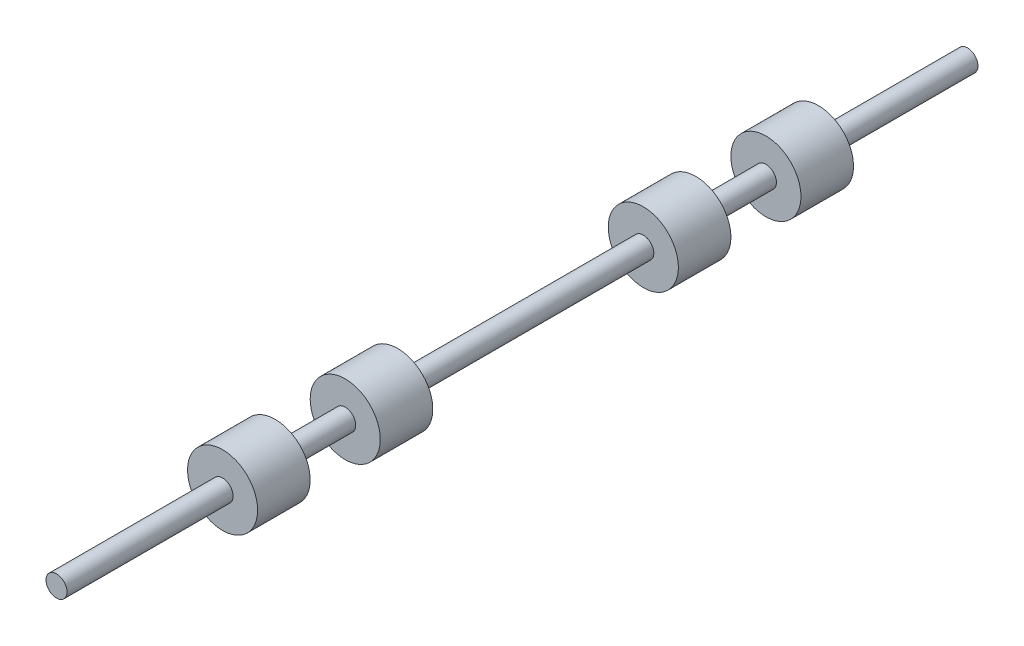
SolidWorks part; units mm, degrees
ref_plane "Front Plane" through (0, 0, 0) normal (0, 0, 1) x (1, 0, 0)
ref_plane "Top Plane" through (0, 0, 0) normal (0, 1, 0) x (1, 0, 0)
ref_plane "Right Plane" through (0, 0, 0) normal (1, 0, 0) x (0, 0, -1)
sketch "Sketch1" plane through (0, 0, 0) normal (0, 0, 1) x (1, 0, 0)
  circle A0 centre (0, 0) radius 0.3
  dimension "D1" = 0.6
extrude "Boss-Extrude1" add sketch "Sketch1" along normal blind 26
sketch "Sketch2" plane through (0, 0, 0) normal (0, 1, 0) x (1, 0, 0)
  line L0 (0, 0) -> (0, -26) construction
  line L1 (-0.3, -26) -> (0.3, -26) construction
  line L2 (0, -6.753) -> (3.292, -6.753) construction
  line L11 (0, -18.76) -> (3.292, -18.76) construction
  line L21 (0, -4.253) -> (1, -4.253)
  line L22 (0, -4.253) -> (0, -5.753)
  line L23 (0, -5.753) -> (1, -5.753)
  line L24 (1, -4.253) -> (1, -5.753)
  line L25 (0, -7.753) -> (1, -7.753)
  line L26 (0, -7.753) -> (0, -9.253)
  line L27 (0, -9.253) -> (1, -9.253)
  line L28 (1, -7.753) -> (1, -9.253)
  line L29 (0, -16.26) -> (1, -16.26)
  line L30 (0, -16.26) -> (0, -17.76)
  line L31 (0, -17.76) -> (1, -17.76)
  line L32 (1, -16.26) -> (1, -17.76)
  line L33 (0, -19.76) -> (1, -19.76)
  line L34 (0, -19.76) -> (0, -21.26)
  line L35 (0, -21.26) -> (1, -21.26)
  line L36 (1, -19.76) -> (1, -21.26)
  dimension "D2" = 12.007
  dimension "D3" = 1
  dimension "D4" = 1.5
  dimension "D5" = 2
  dimension "D6" = 2
  dimension "D7" = 1
  dimension "D8" = 1.5
  dimension "D11" = 7.24
revolve "Revolve1" add sketch "Sketch2" angle 360 about L0
